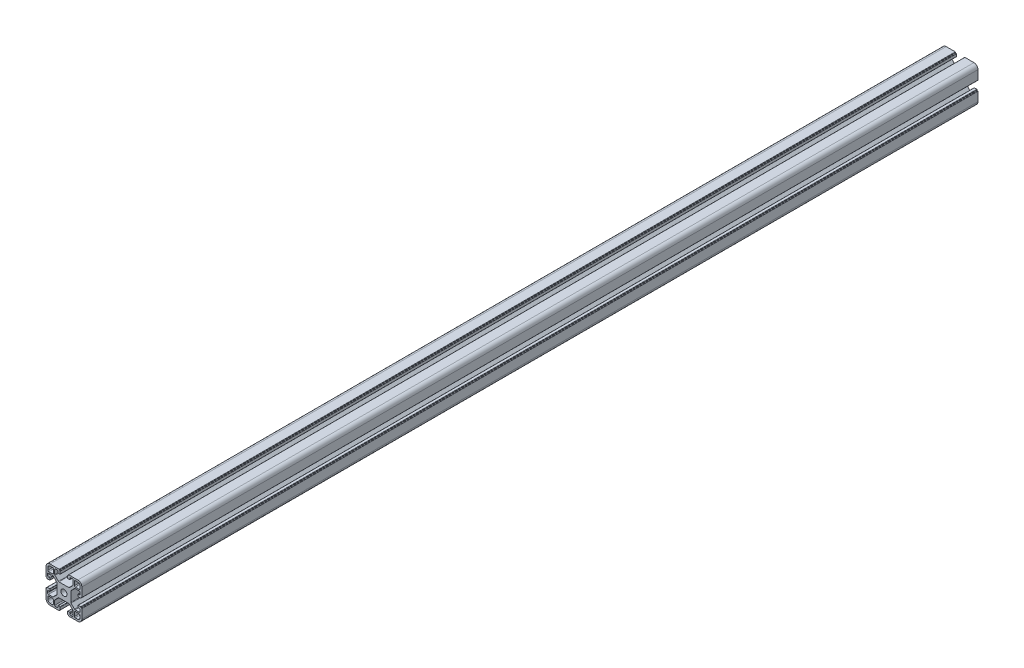
SolidWorks part; units mm, degrees
material "6063 T5"
ref_plane "Спереди" through (0, 0, 0) normal (0, 0, 1) x (1, 0, 0)
ref_plane "Сверху" through (0, 0, 0) normal (0, 1, 0) x (1, 0, 0)
ref_plane "Справа" through (0, 0, 0) normal (1, 0, 0) x (0, 0, -1)
sketch "Эскиз1" plane through (0, 0, 0) normal (0, 0, 1) x (1, 0, 0)
  line L0 (-19.98, 20.5457) -> (20.02, 20.5457) construction
  line L1 (-20, 10.25) -> (-20, 15.5)
  line L2 (-15.5, 20) -> (-10.25, 20)
  line L3 (10.25, 20) -> (15.5, 20)
  line L4 (-12.8, 11.8) -> (-17, 11.8)
  line L5 (-11.8, 12.8) -> (-11.8, 17)
  line L6 (-12.8, 18) -> (-15.5, 18)
  line L7 (-18, 12.8) -> (-18, 15.5)
  line L8 (20, 15.5) -> (20, 10.25)
  line L9 (11.8, 12.8) -> (11.8, 17)
  line L10 (12.8, 11.8) -> (17, 11.8)
  line L11 (18, 12.8) -> (18, 15.5)
  line L12 (12.8, 18) -> (15.5, 18)
  line L13 (20, -10.25) -> (20, -15.5)
  line L14 (15.5, -20) -> (10.25, -20)
  line L15 (12.8, -11.8) -> (17, -11.8)
  line L16 (11.8, -12.8) -> (11.8, -17)
  line L17 (12.8, -18) -> (15.5, -18)
  line L18 (18, -12.8) -> (18, -15.5)
  line L19 (-10.25, -20) -> (-15.5, -20)
  line L20 (-20, -15.5) -> (-20, -10.25)
  line L21 (-11.8, -12.8) -> (-11.8, -17)
  line L22 (-12.8, -11.8) -> (-17, -11.8)
  line L23 (-18, -12.8) -> (-18, -15.5)
  line L24 (-12.8, -18) -> (-15.5, -18)
  line L25 (0, 0) -> (-11.8, 12.8) construction
  arc A0 (-20, 15.5) -> (-15.5, 20) centre (-15.5, 15.5) cw
  arc A1 (-15.5, 18) -> (-18, 15.5) centre (-15.5, 15.5) ccw
  arc A2 (-17, 11.8) -> (-18, 12.8) centre (-17, 12.8) cw
  arc A3 (-12.8, 11.8) -> (-11.8, 12.8) centre (-12.8, 12.8) ccw
  arc A4 (-11.8, 17) -> (-12.8, 18) centre (-12.8, 17) ccw
  circle A5 centre (0, 0) radius 3.4
  arc A6 (15.5, 20) -> (20, 15.5) centre (15.5, 15.5) cw
  arc A7 (18, 15.5) -> (15.5, 18) centre (15.5, 15.5) ccw
  arc A8 (11.8, 17) -> (12.8, 18) centre (12.8, 17) cw
  arc A9 (11.8, 12.8) -> (12.8, 11.8) centre (12.8, 12.8) ccw
  arc A10 (17, 11.8) -> (18, 12.8) centre (17, 12.8) ccw
  arc A11 (20, -15.5) -> (15.5, -20) centre (15.5, -15.5) cw
  arc A12 (15.5, -18) -> (18, -15.5) centre (15.5, -15.5) ccw
  arc A13 (17, -11.8) -> (18, -12.8) centre (17, -12.8) cw
  arc A14 (12.8, -11.8) -> (11.8, -12.8) centre (12.8, -12.8) ccw
  arc A15 (11.8, -17) -> (12.8, -18) centre (12.8, -17) ccw
  arc A16 (-15.5, -20) -> (-20, -15.5) centre (-15.5, -15.5) cw
  arc A17 (-18, -15.5) -> (-15.5, -18) centre (-15.5, -15.5) ccw
  arc A18 (-11.8, -17) -> (-12.8, -18) centre (-12.8, -17) cw
  arc A19 (-11.8, -12.8) -> (-12.8, -11.8) centre (-12.8, -12.8) ccw
  arc A20 (-17, -11.8) -> (-18, -12.8) centre (-17, -12.8) ccw
  point P5 (0, 0)
  line B0 (-20, 10.25) -> (-20, 5.4)
  line B1 (-19.7, 5.1) -> (-19.3, 5.1)
  line B2 (-19, 4.8) -> (-19, 4.4)
  line B3 (-18.7, 4.1) -> (-16, 4.1)
  line B4 (-15.7, 4.4) -> (-15.7, 6.3)
  line B5 (-16, 6.6) -> (-17.2, 6.6)
  line B6 (-18.2, 7.6) -> (-18.2, 9.25)
  line B7 (-17.2, 10.25) -> (-12.4642, 10.25)
  line B8 (-11.7571, 9.9571) -> (-7.9929, 6.1929)
  line B9 (-7.7, 5.4858) -> (-7.7, -5.4858)
  line B10 (-7.7, 0) -> (-20, 0) construction
  line B11 (-11.7571, -9.9571) -> (-7.9929, -6.1929)
  line B12 (-17.2, -10.25) -> (-12.4642, -10.25)
  line B13 (-18.2, -7.6) -> (-18.2, -9.25)
  line B14 (-16, -6.6) -> (-17.2, -6.6)
  line B15 (-15.7, -4.4) -> (-15.7, -6.3)
  line B16 (-18.7, -4.1) -> (-16, -4.1)
  line B17 (-19, -4.8) -> (-19, -4.4)
  line B18 (-19.7, -5.1) -> (-19.3, -5.1)
  line B19 (-20, -10.25) -> (-20, -5.4)
  arc B20 (-15.7, 6.3) -> (-16, 6.6) centre (-16, 6.3) ccw
  arc B21 (-16, 4.1) -> (-15.7, 4.4) centre (-16, 4.4) ccw
  arc B22 (-19, 4.4) -> (-18.7, 4.1) centre (-18.7, 4.4) ccw
  arc B23 (-19.3, 5.1) -> (-19, 4.8) centre (-19.3, 4.8) cw
  arc B24 (-20, 5.4) -> (-19.7, 5.1) centre (-19.7, 5.4) ccw
  arc B25 (-7.9929, 6.1929) -> (-7.7, 5.4858) centre (-8.7, 5.4858) cw
  arc B26 (-12.4642, 10.25) -> (-11.7571, 9.9571) centre (-12.4642, 9.25) cw
  arc B27 (-18.2, 9.25) -> (-17.2, 10.25) centre (-17.2, 9.25) cw
  arc B28 (-17.2, 6.6) -> (-18.2, 7.6) centre (-17.2, 7.6) cw
  arc B29 (-17.2, -6.6) -> (-18.2, -7.6) centre (-17.2, -7.6) ccw
  arc B30 (-18.2, -9.25) -> (-17.2, -10.25) centre (-17.2, -9.25) ccw
  arc B31 (-12.4642, -10.25) -> (-11.7571, -9.9571) centre (-12.4642, -9.25) ccw
  arc B32 (-7.9929, -6.1929) -> (-7.7, -5.4858) centre (-8.7, -5.4858) ccw
  arc B33 (-20, -5.4) -> (-19.7, -5.1) centre (-19.7, -5.4) cw
  arc B34 (-19.3, -5.1) -> (-19, -4.8) centre (-19.3, -4.8) ccw
  arc B35 (-19, -4.4) -> (-18.7, -4.1) centre (-18.7, -4.4) cw
  arc B36 (-16, -4.1) -> (-15.7, -4.4) centre (-16, -4.4) cw
  arc B37 (-15.7, -6.3) -> (-16, -6.6) centre (-16, -6.3) cw
  line B38 (10.25, 20) -> (5.4, 20)
  line B39 (5.1, 19.7) -> (5.1, 19.3)
  line B40 (4.8, 19) -> (4.4, 19)
  line B41 (4.1, 18.7) -> (4.1, 16)
  line B42 (4.4, 15.7) -> (6.3, 15.7)
  line B43 (6.6, 16) -> (6.6, 17.2)
  line B44 (7.6, 18.2) -> (9.25, 18.2)
  line B45 (10.25, 17.2) -> (10.25, 12.4642)
  line B46 (9.9571, 11.7571) -> (6.1929, 7.9929)
  line B47 (5.4858, 7.7) -> (-5.4858, 7.7)
  line B48 (0, 7.7) -> (0, 20) construction
  line B49 (-9.9571, 11.7571) -> (-6.1929, 7.9929)
  line B50 (-10.25, 17.2) -> (-10.25, 12.4642)
  line B51 (-7.6, 18.2) -> (-9.25, 18.2)
  line B52 (-6.6, 16) -> (-6.6, 17.2)
  line B53 (-4.4, 15.7) -> (-6.3, 15.7)
  line B54 (-4.1, 18.7) -> (-4.1, 16)
  line B55 (-4.8, 19) -> (-4.4, 19)
  line B56 (-5.1, 19.7) -> (-5.1, 19.3)
  line B57 (-10.25, 20) -> (-5.4, 20)
  arc B58 (6.3, 15.7) -> (6.6, 16) centre (6.3, 16) ccw
  arc B59 (4.1, 16) -> (4.4, 15.7) centre (4.4, 16) ccw
  arc B60 (4.4, 19) -> (4.1, 18.7) centre (4.4, 18.7) ccw
  arc B61 (5.1, 19.3) -> (4.8, 19) centre (4.8, 19.3) cw
  arc B62 (5.4, 20) -> (5.1, 19.7) centre (5.4, 19.7) ccw
  arc B63 (6.1929, 7.9929) -> (5.4858, 7.7) centre (5.4858, 8.7) cw
  arc B64 (10.25, 12.4642) -> (9.9571, 11.7571) centre (9.25, 12.4642) cw
  arc B65 (9.25, 18.2) -> (10.25, 17.2) centre (9.25, 17.2) cw
  arc B66 (6.6, 17.2) -> (7.6, 18.2) centre (7.6, 17.2) cw
  arc B67 (-6.6, 17.2) -> (-7.6, 18.2) centre (-7.6, 17.2) ccw
  arc B68 (-9.25, 18.2) -> (-10.25, 17.2) centre (-9.25, 17.2) ccw
  arc B69 (-10.25, 12.4642) -> (-9.9571, 11.7571) centre (-9.25, 12.4642) ccw
  arc B70 (-6.1929, 7.9929) -> (-5.4858, 7.7) centre (-5.4858, 8.7) ccw
  arc B71 (-5.4, 20) -> (-5.1, 19.7) centre (-5.4, 19.7) cw
  arc B72 (-5.1, 19.3) -> (-4.8, 19) centre (-4.8, 19.3) ccw
  arc B73 (-4.4, 19) -> (-4.1, 18.7) centre (-4.4, 18.7) cw
  arc B74 (-4.1, 16) -> (-4.4, 15.7) centre (-4.4, 16) cw
  arc B75 (-6.3, 15.7) -> (-6.6, 16) centre (-6.3, 16) cw
  line B76 (20, -10.25) -> (20, -5.4)
  line B77 (19.7, -5.1) -> (19.3, -5.1)
  line B78 (19, -4.8) -> (19, -4.4)
  line B79 (18.7, -4.1) -> (16, -4.1)
  line B80 (15.7, -4.4) -> (15.7, -6.3)
  line B81 (16, -6.6) -> (17.2, -6.6)
  line B82 (18.2, -7.6) -> (18.2, -9.25)
  line B83 (17.2, -10.25) -> (12.4642, -10.25)
  line B84 (11.7571, -9.9571) -> (7.9929, -6.1929)
  line B85 (7.7, -5.4858) -> (7.7, 5.4858)
  line B86 (7.7, 0) -> (20, 0) construction
  line B87 (11.7571, 9.9571) -> (7.9929, 6.1929)
  line B88 (17.2, 10.25) -> (12.4642, 10.25)
  line B89 (18.2, 7.6) -> (18.2, 9.25)
  line B90 (16, 6.6) -> (17.2, 6.6)
  line B91 (15.7, 4.4) -> (15.7, 6.3)
  line B92 (18.7, 4.1) -> (16, 4.1)
  line B93 (19, 4.8) -> (19, 4.4)
  line B94 (19.7, 5.1) -> (19.3, 5.1)
  line B95 (20, 10.25) -> (20, 5.4)
  arc B96 (15.7, -6.3) -> (16, -6.6) centre (16, -6.3) ccw
  arc B97 (16, -4.1) -> (15.7, -4.4) centre (16, -4.4) ccw
  arc B98 (19, -4.4) -> (18.7, -4.1) centre (18.7, -4.4) ccw
  arc B99 (19.3, -5.1) -> (19, -4.8) centre (19.3, -4.8) cw
  arc B100 (20, -5.4) -> (19.7, -5.1) centre (19.7, -5.4) ccw
  arc B101 (7.9929, -6.1929) -> (7.7, -5.4858) centre (8.7, -5.4858) cw
  arc B102 (12.4642, -10.25) -> (11.7571, -9.9571) centre (12.4642, -9.25) cw
  arc B103 (18.2, -9.25) -> (17.2, -10.25) centre (17.2, -9.25) cw
  arc B104 (17.2, -6.6) -> (18.2, -7.6) centre (17.2, -7.6) cw
  arc B105 (17.2, 6.6) -> (18.2, 7.6) centre (17.2, 7.6) ccw
  arc B106 (18.2, 9.25) -> (17.2, 10.25) centre (17.2, 9.25) ccw
  arc B107 (12.4642, 10.25) -> (11.7571, 9.9571) centre (12.4642, 9.25) ccw
  arc B108 (7.9929, 6.1929) -> (7.7, 5.4858) centre (8.7, 5.4858) ccw
  arc B109 (20, 5.4) -> (19.7, 5.1) centre (19.7, 5.4) cw
  arc B110 (19.3, 5.1) -> (19, 4.8) centre (19.3, 4.8) ccw
  arc B111 (19, 4.4) -> (18.7, 4.1) centre (18.7, 4.4) cw
  arc B112 (16, 4.1) -> (15.7, 4.4) centre (16, 4.4) cw
  arc B113 (15.7, 6.3) -> (16, 6.6) centre (16, 6.3) cw
  line B114 (-10.25, -20) -> (-5.4, -20)
  line B115 (-5.1, -19.7) -> (-5.1, -19.3)
  line B116 (-4.8, -19) -> (-4.4, -19)
  line B117 (-4.1, -18.7) -> (-4.1, -16)
  line B118 (-4.4, -15.7) -> (-6.3, -15.7)
  line B119 (-6.6, -16) -> (-6.6, -17.2)
  line B120 (-7.6, -18.2) -> (-9.25, -18.2)
  line B121 (-10.25, -17.2) -> (-10.25, -12.4642)
  line B122 (-9.9571, -11.7571) -> (-6.1929, -7.9929)
  line B123 (-5.4858, -7.7) -> (5.4858, -7.7)
  line B124 (0, -7.7) -> (0, -20) construction
  line B125 (9.9571, -11.7571) -> (6.1929, -7.9929)
  line B126 (10.25, -17.2) -> (10.25, -12.4642)
  line B127 (7.6, -18.2) -> (9.25, -18.2)
  line B128 (6.6, -16) -> (6.6, -17.2)
  line B129 (4.4, -15.7) -> (6.3, -15.7)
  line B130 (4.1, -18.7) -> (4.1, -16)
  line B131 (4.8, -19) -> (4.4, -19)
  line B132 (5.1, -19.7) -> (5.1, -19.3)
  line B133 (10.25, -20) -> (5.4, -20)
  arc B134 (-6.3, -15.7) -> (-6.6, -16) centre (-6.3, -16) ccw
  arc B135 (-4.1, -16) -> (-4.4, -15.7) centre (-4.4, -16) ccw
  arc B136 (-4.4, -19) -> (-4.1, -18.7) centre (-4.4, -18.7) ccw
  arc B137 (-5.1, -19.3) -> (-4.8, -19) centre (-4.8, -19.3) cw
  arc B138 (-5.4, -20) -> (-5.1, -19.7) centre (-5.4, -19.7) ccw
  arc B139 (-6.1929, -7.9929) -> (-5.4858, -7.7) centre (-5.4858, -8.7) cw
  arc B140 (-10.25, -12.4642) -> (-9.9571, -11.7571) centre (-9.25, -12.4642) cw
  arc B141 (-9.25, -18.2) -> (-10.25, -17.2) centre (-9.25, -17.2) cw
  arc B142 (-6.6, -17.2) -> (-7.6, -18.2) centre (-7.6, -17.2) cw
  arc B143 (6.6, -17.2) -> (7.6, -18.2) centre (7.6, -17.2) ccw
  arc B144 (9.25, -18.2) -> (10.25, -17.2) centre (9.25, -17.2) ccw
  arc B145 (10.25, -12.4642) -> (9.9571, -11.7571) centre (9.25, -12.4642) ccw
  arc B146 (6.1929, -7.9929) -> (5.4858, -7.7) centre (5.4858, -8.7) ccw
  arc B147 (5.4, -20) -> (5.1, -19.7) centre (5.4, -19.7) cw
  arc B148 (5.1, -19.3) -> (4.8, -19) centre (4.8, -19.3) ccw
  arc B149 (4.4, -19) -> (4.1, -18.7) centre (4.4, -18.7) cw
  arc B150 (4.1, -16) -> (4.4, -15.7) centre (4.4, -16) cw
  arc B151 (6.3, -15.7) -> (6.6, -16) centre (6.3, -16) cw
  dimension "D2" = 4.5
  dimension "D3" = 2.5
  dimension "D5" = 1
  dimension "D6" = 6.8
  dimension "D1" = 20
  dimension "D4" = 6.2
sketch_block_instance "8B(20,5PL)-1"
sketch_block "8B(20,5PL)" parameters "D7"=0.3, "D8"=1, "D1"=12.3, "D2"=4.3, "D3"=8.2, "D4"=20.5, "D5"=10.2, "D6"=135
sketch_block_instance "8B(20,5PL)-3"
sketch_block_instance "8B(20,5PL)-4"
sketch_block_instance "8B(20,5PL)-5"
extrude "Бобышка-Вытянуть1" add sketch "Эскиз1" along normal blind 1000 contours B151 B129 B150 B130 B149 B131 B148 B132 B147 B133 L14 A11 L13 B76 B100 B77 B99 B78 B98 B79 B97 B80 B96 B81 B104 B82 B103 B83 B102 B84 B101 B85 B108 B87 B107 B88 B106 B89 B105 B90 B113 B91 B112 B92 B111 B93 B110 B94 B109 B95 L8
